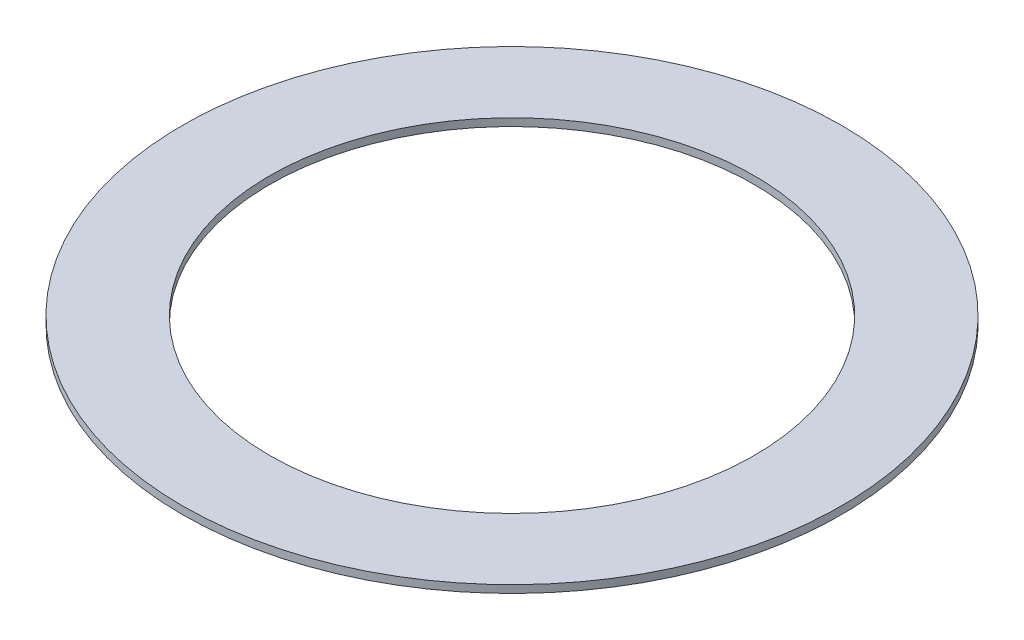
SolidWorks part; units mm, degrees
material "Oak"
ref_plane "Front Plane" through (0, 0, 0) normal (0, 0, 1) x (1, 0, 0)
ref_plane "Top Plane" through (0, 0, 0) normal (0, 1, 0) x (1, 0, 0)
ref_plane "Right Plane" through (0, 0, 0) normal (1, 0, 0) x (0, 0, -1)
sketch "Sketch1" plane through (0, 0, 0) normal (0, 1, 0) x (1, 0, 0)
  circle A0 centre (0, 0) radius 76.2
  circle A1 centre (0, 0) radius 103.632
  dimension "D1" = 152.4
  dimension "D2" = 207.264
extrude "Boss-Extrude1" add sketch "Sketch1" along normal blind 2.4
